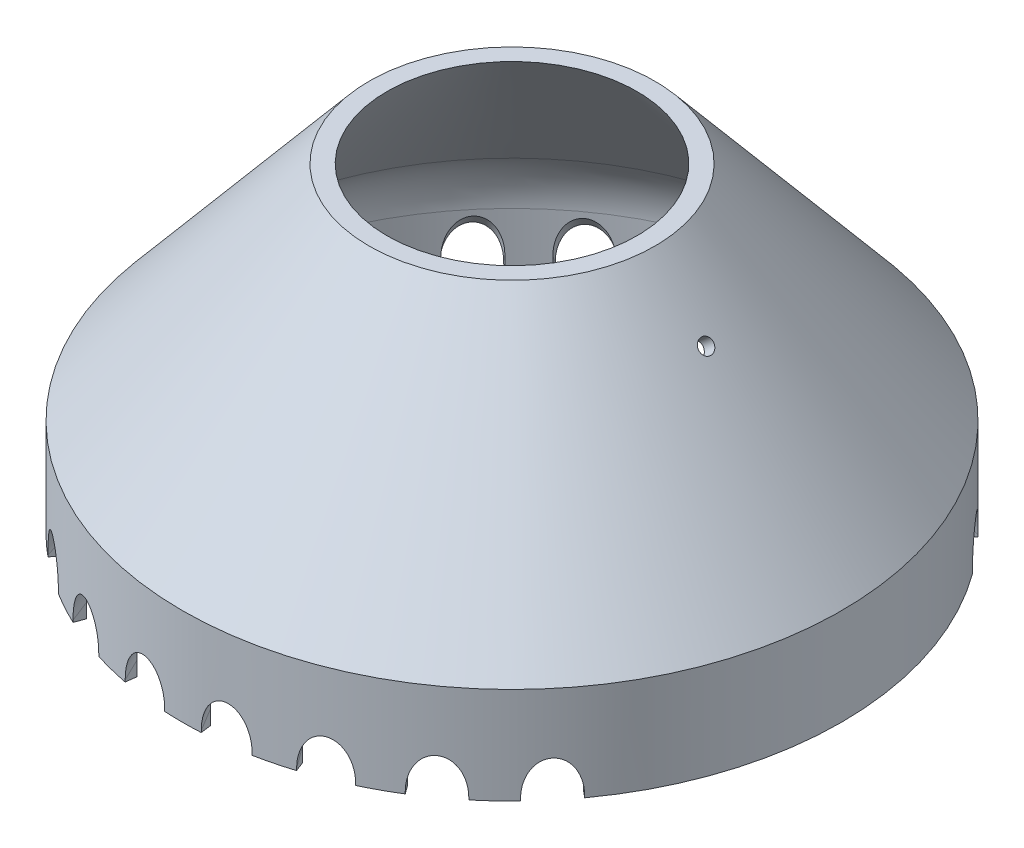
SolidWorks part; units mm, degrees
ref_plane "Front Plane" through (0, 0, 0) normal (0, 0, 1) x (1, 0, 0)
ref_plane "Top Plane" through (0, 0, 0) normal (0, 1, 0) x (1, 0, 0)
ref_plane "Right Plane" through (0, 0, 0) normal (1, 0, 0) x (0, 0, -1)
sketch "Cone Cross Section" plane through (0, 0, 0) normal (0, 0, -1) x (1, 0, 0)
  line L0 (0, 0) -> (13.7186, 0) construction
  line L1 (13.7186, 0) -> (32.6604, 22.5741)
  line L2 (35, 25.3622) -> (36.1491, 24.3981) construction
  line L3 (13.7186, 0) -> (15.6767, 0)
  line L4 (36.1491, 24.3981) -> (15.6767, 0)
  line L5 (35, 29.0019) -> (35, 35)
  line L6 (0, 0) -> (0, 15.7221) construction
  line L7 (35, 35) -> (36.1491, 35)
  line L8 (36.1491, 35) -> (36.1491, 24.3981)
  arc A0 (32.6604, 22.5741) -> (35, 29.0019) centre (25, 29.0019) ccw
  dimension "D6" = 10
  dimension "D1" = 35
  dimension "D2" = 25.3622
  dimension "D3" = 1.5
  dimension "D4" = 35
  dimension "D5" = 1.1491
  dimension "D7" = 10.6019
revolve "Revolve1" add sketch "Cone Cross Section" angle 360 about L6
sketch "Support Hole Plane Def Line" plane through (0, 0, 0) normal (0, 1, 0) x (1, 0, 0)
  line L0 (13.7186, 5) -> (13.7186, -5)
  line L1 (0, 0) -> (-13.7186, 0) construction
  line L3 (-13.7186, 5) -> (-13.7186, -5)
  line L4 (0, 0) -> (13.7186, 0) construction
  dimension "D1" = 10
ref_plane "Support Hole Plane 1" through (8.0504, 6.7551, 0) normal (-0.766, -0.6428, 0) x (0, 0, 1)
ref_plane "Support Hole Plane 2" through (-8.0504, 6.7551, 0) normal (0.766, -0.6428, 0) x (0, 0, -1)
sketch "Sketch3" plane through (8.0504, 6.7551, 0) normal (-0.766, -0.6428, 0) x (0, 0, 1)
  line L0 (0, -18.8181) -> (0, -8.8181) construction
  circle A0 centre (0, -18.8181) radius 0.8064
sketch "Sketch4" plane through (-8.0504, 6.7551, 0) normal (-0.766, 0.6428, 0) x (0, 0, 1)
  line L0 (0, -18.8181) -> (0, -8.8181) construction
  circle A0 centre (0, -18.8181) radius 0.8064
extrude "Support Hole 1" cut sketch "Sketch4" along normal up to next and the other way up to next
extrude "Support Hole 2" cut sketch "Sketch3" along normal up to next and the other way up to next
sketch "Sketch5" plane through (7.7889, -12.1174, 6.5357) normal (-0.4924, 0.766, -0.4132) x (0.8704, 0.4334, -0.2338)
  line L1 (3.5458, -3.8839) -> (1.4293, -5.8161) construction
  line L3 (4.9663, -7.6647) -> (6.0741, -6.6534) construction
  line L4 (1.6995, -5.5695) -> (-1.6717, -1.8769)
  line L5 (-1.6717, -1.8769) -> (2.0209, 1.4943)
  line L9 (2.0209, 1.4943) -> (5.3921, -2.1984)
  line L10 (7.1819, -5.642) -> (2.4623, -0.4724) construction
  arc A0 (1.6995, -5.5695) -> (5.3921, -2.1984) centre (3.5458, -3.8839) ccw
  dimension "D1" = 5
  dimension "D2" = 5
extrude "Turn Tool Channel" cut sketch "Sketch5" against normal up to next
ref_plane "Plane4" through (0, -10.826, 0) normal (0, -1, 0) x (-0.766, 0, -0.6428)
sketch "KeyPieceRotationArcCopy" plane through (0, -10.826, 0) normal (0, -1, 0) x (-0.766, 0, -0.6428)
  arc A0 (-11.7067, 0) -> (2.0328, -11.5288) centre (0, 0) ccw construction
  arc A1 (-11.7067, 0) -> (2.0328, -11.5288) centre (0, 0) ccw
pattern_curve "CrvPattern2" of "Turn Tool Channel" parameters "D1"=8, "D3"=50, "D2"=1, "D4"=50
ref_plane "Center Mirror Plane" through (0, 0, 0) normal (0, 0, 1) x (1, 0, 0)
mirror "Mirror1" about plane through (0, 0, 0) normal (0, 0, 1) of "Turn Tool Channel", "CrvPattern2"
equation "\"ConeAngle\"= \"KeyAngle@drive_circle_16_mcube.SLDPRT\""
equation "\"ConeBase\"= \"ConeBaseRadius@Outer Cone Spacer@drive_circle_16_mcube.SLDPRT\""
equation "\"ConeHoleHeight\"= \"ConeHoleHeight@drive_circle_16_mcube.SLDPRT\""
